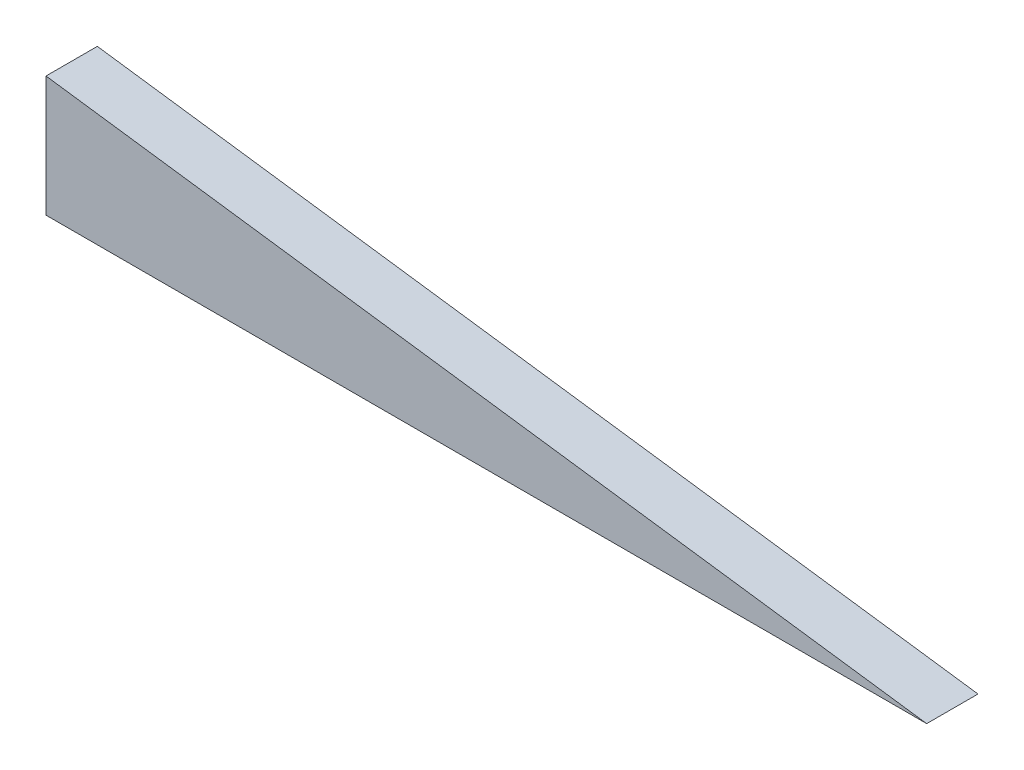
SolidWorks part; units mm, degrees
ref_plane "Front Plane" through (0, 0, 0) normal (0, 0, 1) x (1, 0, 0)
ref_plane "Top Plane" through (0, 0, 0) normal (0, 1, 0) x (1, 0, 0)
ref_plane "Right Plane" through (0, 0, 0) normal (1, 0, 0) x (0, 0, -1)
sketch "Sketch1" plane through (0, 0, 0) normal (0, 0, 1) x (1, 0, 0)
  line L0 (0, 0) -> (-108.966, 0)
  line L1 (-108.966, 14.9148) -> (0, 0)
  line L2 (-108.966, 0) -> (-108.966, 14.9148)
  dimension "D1" = 109.982
  dimension "D2" = 108.966
extrude "Boss-Extrude1" add sketch "Sketch1" along normal mid plane 6.35
equation "\"material\"=\"GMaterial@Platform.assembly\""
equation "\"D1@Boss-Extrude1\"=\"material\""
